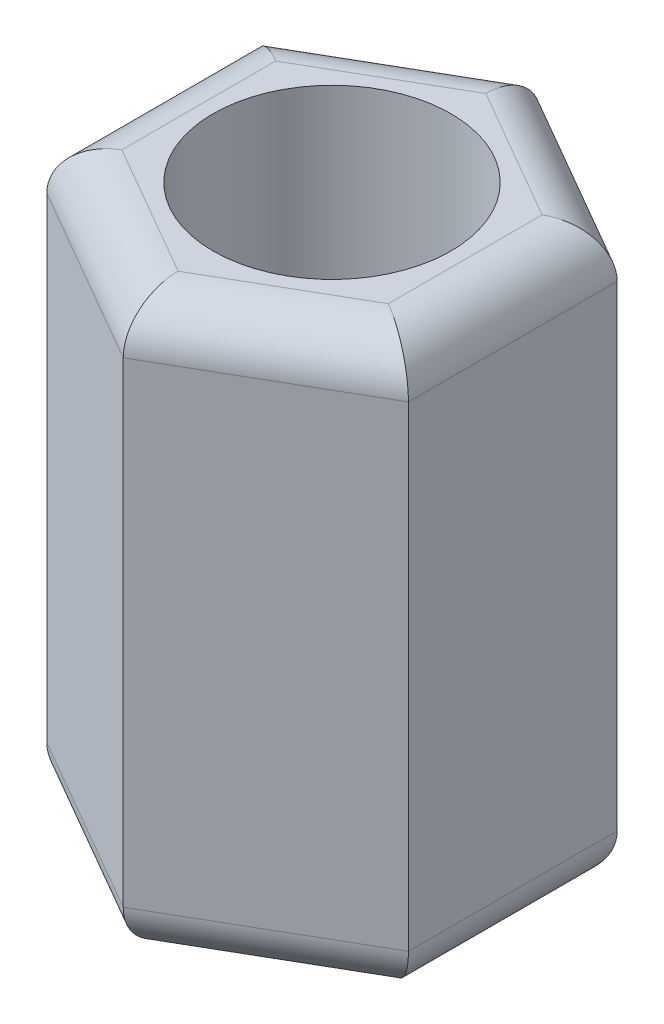
SolidWorks part; units mm, degrees
ref_plane "前视基准面" through (0, 0, 0) normal (0, 0, 1) x (1, 0, 0)
ref_plane "上视基准面" through (0, 0, 0) normal (0, 1, 0) x (1, 0, 0)
ref_plane "右视基准面" through (0, 0, 0) normal (1, 0, 0) x (0, 0, -1)
sketch "草图1" plane through (0, 0, 0) normal (0, 1, 0) x (1, 0, 0)
  line L1 (1.9, -1.097) -> (1.9, 1.097)
  line L2 (1.9, 1.097) -> (0, 2.1939)
  line L3 (0, 2.1939) -> (-1.9, 1.097)
  line L4 (-1.9, 1.097) -> (-1.9, -1.097)
  line L5 (-1.9, -1.097) -> (0, -2.1939)
  line L6 (0, -2.1939) -> (1.9, -1.097)
  circle A0 centre (0, 0) radius 1.9 construction
  circle A1 centre (0, 0) radius 1.25
  dimension "D2" = 2.5
  dimension "D1" = 3.8
extrude "凸台-拉伸1" add sketch "草图1" along normal blind 6
fillet "圆角1" radius 0.5 12 edges at (-0.95, 6, 1.6454) (-1.9, 6, 0) (-0.95, 6, -1.6454) (0.95, 6, -1.6454) (1.9, 6, 0) (0.95, 6, 1.6454) (-0.95, 0, 1.6454) (0.95, 0, 1.6454) (1.9, 0, 0) (0.95, 0, -1.6454) (-0.95, 0, -1.6454) (-1.9, 0, 0)
